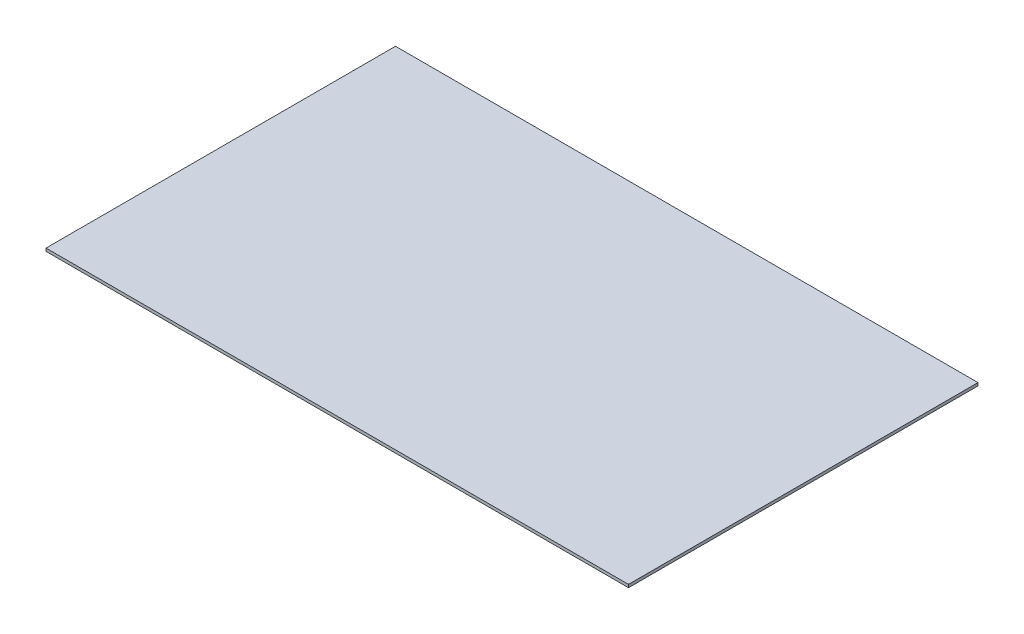
SolidWorks part; units mm, degrees
material "Balsa"
ref_plane "Front Plane" through (0, 0, 0) normal (0, 0, 1) x (1, 0, 0)
ref_plane "Top Plane" through (0, 0, 0) normal (0, 1, 0) x (1, 0, 0)
ref_plane "Right Plane" through (0, 0, 0) normal (1, 0, 0) x (0, 0, -1)
sketch "Sketch1" plane through (0, 0, 0) normal (0, 1, 0) x (1, 0, 0)
  line L1 (-254, -152.4) -> (254, -152.4)
  line L2 (-254, -152.4) -> (-254, 152.4)
  line L3 (-254, 152.4) -> (254, 152.4)
  line L4 (254, -152.4) -> (254, 152.4)
  line L5 (-254, -152.4) -> (254, 152.4) construction
  line L6 (-254, 152.4) -> (254, -152.4) construction
  point P0 (0, 0)
  dimension "D1" = 304.8
  dimension "D2" = 508
extrude "New Board 12x22in" add sketch "Sketch1" along normal blind 2.54
